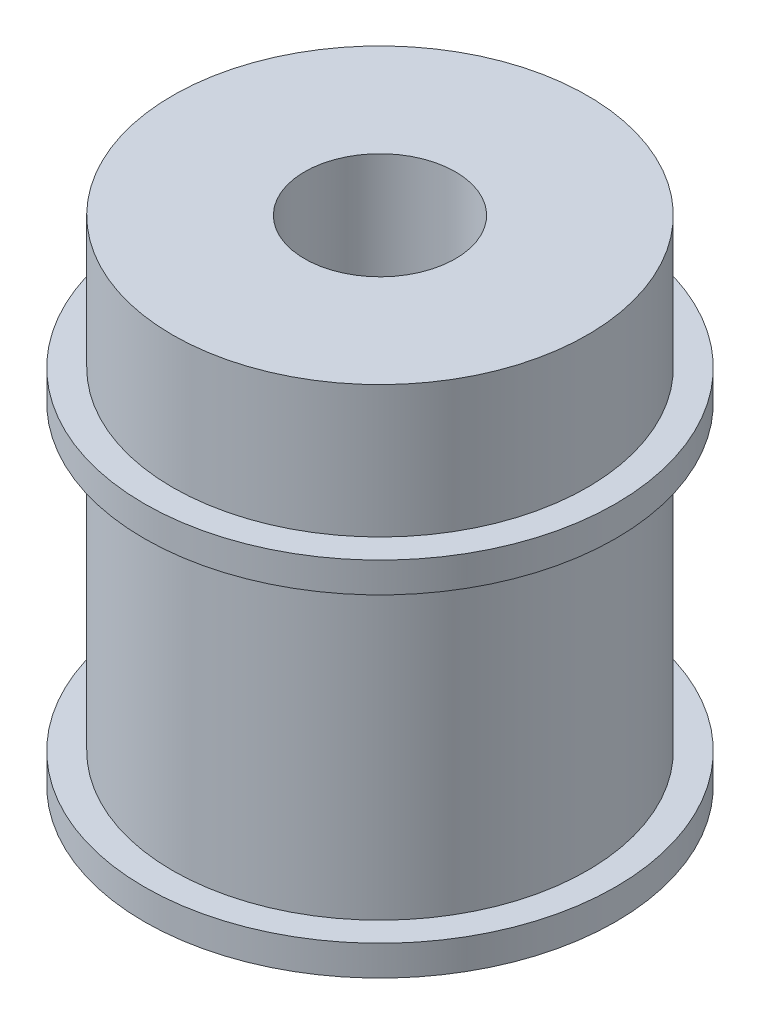
SolidWorks part; units mm, degrees
ref_plane "Front Plane" through (0, 0, 0) normal (0, 0, 1) x (1, 0, 0)
ref_plane "Top Plane" through (0, 0, 0) normal (0, 1, 0) x (1, 0, 0)
ref_plane "Right Plane" through (0, 0, 0) normal (1, 0, 0) x (0, 0, -1)
sketch "Sketch1" plane through (0, 0, 0) normal (0, 1, 0) x (1, 0, 0)
  circle A0 centre (0, 0) radius 12.5
  dimension "D1" = 25
extrude "Boss-Extrude1" add sketch "Sketch1" along normal blind 1.6
sketch "Sketch2" plane through (0, 1.6, 0) normal (0, 1, 0) x (1, 0, 0)
  circle A0 centre (0, 0) radius 11
  dimension "D1" = 22
extrude "Boss-Extrude2" add sketch "Sketch2" along normal blind 16
sketch "Sketch3" plane through (0, 17.6, 0) normal (0, 1, 0) x (1, 0, 0)
  circle A0 centre (0, 0) radius 12.5
  dimension "D1" = 25
extrude "Boss-Extrude3" add sketch "Sketch3" along normal blind 1.6
sketch "Sketch4" plane through (0, 19.2, 0) normal (0, 1, 0) x (1, 0, 0)
  circle A0 centre (0, 0) radius 11
  dimension "D1" = 22
extrude "Boss-Extrude4" add sketch "Sketch4" along normal blind 7
sketch "Sketch5" plane through (0, 0, 0) normal (0, -1, 0) x (1, 0, 0)
  circle A0 centre (0, 0) radius 4
  dimension "D1" = 8
extrude "Cut-Extrude1" cut sketch "Sketch5" against normal through all
